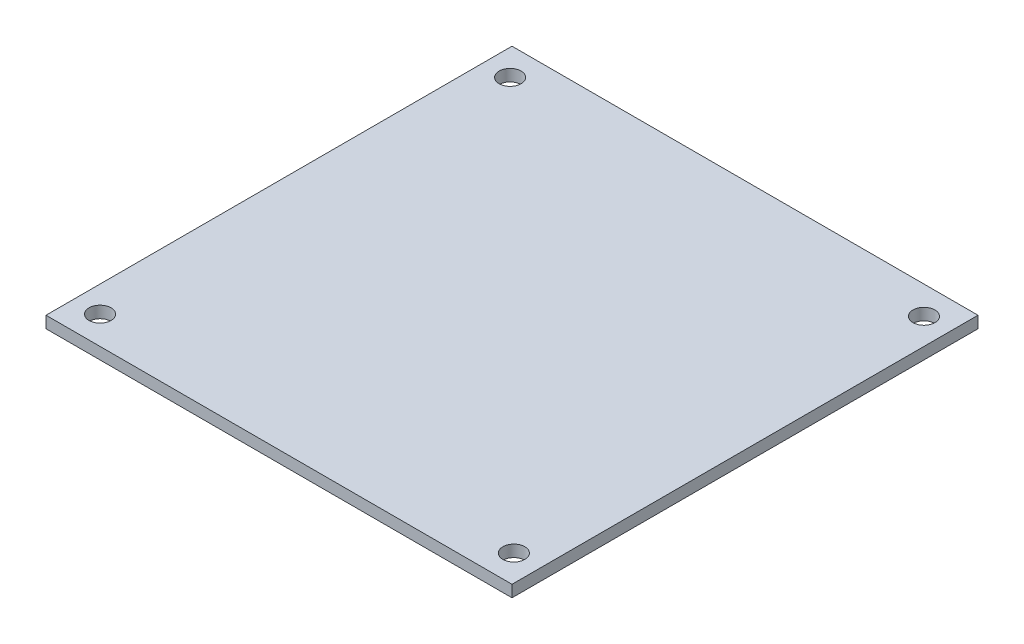
SolidWorks part; units mm, degrees
ref_plane "Front Plane" through (0, 0, 0) normal (0, 0, 1) x (1, 0, 0)
ref_plane "Top Plane" through (0, 0, 0) normal (0, 1, 0) x (1, 0, 0)
ref_plane "Right Plane" through (0, 0, 0) normal (1, 0, 0) x (0, 0, -1)
sketch "Sketch1" plane through (0, 0, 0) normal (0, 1, 0) x (1, 0, 0)
  line L0 (31.75, 0) -> (-31.75, 0) construction
  line L1 (31.75, -31.75) -> (-31.75, -31.75)
  line L2 (31.75, -31.75) -> (31.75, 31.75)
  line L3 (31.75, 31.75) -> (-31.75, 31.75)
  line L4 (-31.75, -31.75) -> (-31.75, 31.75)
  line L5 (31.75, -31.75) -> (-31.75, 31.75) construction
  line L6 (31.75, 31.75) -> (-31.75, -31.75) construction
  line L7 (0, -31.75) -> (0, 31.75) construction
  line L8 (-28.194, 27.94) -> (28.194, 27.94) construction
  circle A0 centre (-28.194, 27.94) radius 1.5
  circle A1 centre (28.194, 27.94) radius 1.5
  circle A2 centre (28.194, -27.94) radius 1.5
  circle A3 centre (-28.194, -27.94) radius 1.5
  point P0 (0, 0)
  point P9 (0, 0)
  point P12 (0, 0)
  point P14 (0, 27.94)
  dimension "D5" = 3
  dimension "D1" = 63.5
  dimension "D2" = 63.5
  dimension "D3" = 56.388
  dimension "D4" = 3.81
extrude "Boss-Extrude1" add sketch "Sketch1" along normal blind 1.6
